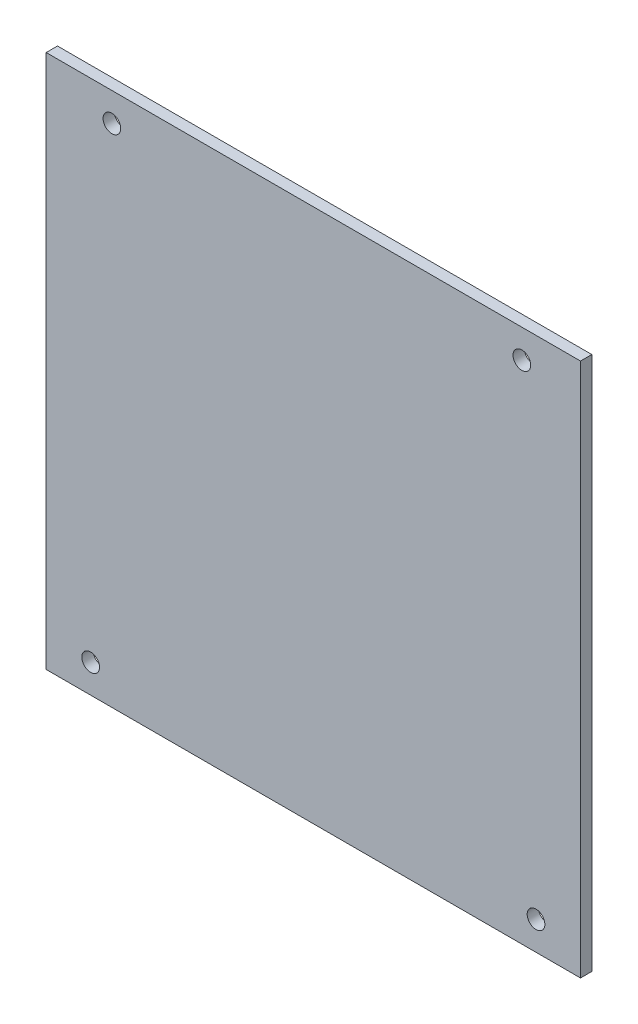
SolidWorks part; units mm, degrees
material "5052-H32"
ref_plane "Front Plane" through (0, 0, 0) normal (0, 0, 1) x (1, 0, 0)
ref_plane "Top Plane" through (0, 0, 0) normal (0, 1, 0) x (1, 0, 0)
ref_plane "Right Plane" through (0, 0, 0) normal (1, 0, 0) x (0, 0, -1)
sketch "Sketch3" plane through (0, 0, 0) normal (0, 0, 1) x (1, 0, 0)
  line L0 (-46.984, 48) -> (-46.984, -48) construction
  line L1 (-48, -48) -> (48, -48)
  line L2 (-48, -48) -> (-48, 48)
  line L3 (-48, 48) -> (48, 48)
  line L4 (48, -48) -> (48, 48)
  line L5 (-48, -48) -> (48, 48) construction
  line L6 (-48, 48) -> (48, -48) construction
  line L7 (45.968, 48) -> (45.968, -48) construction
  circle A4 centre (40.005, -42.865) radius 1.59 construction
  circle A5 centre (37.465, 42.865) radius 1.59 construction
  circle A6 centre (-36.195, 42.865) radius 1.59 construction
  circle A7 centre (-40.005, -42.865) radius 1.59 construction
  circle A8 centre (40.005, -42.865) radius 1.59
  circle A9 centre (37.465, 42.865) radius 1.59
  circle A10 centre (-36.195, 42.865) radius 1.59
  circle A11 centre (-40.005, -42.865) radius 1.59
  point P0 (0, 0)
  dimension "D1" = 96
  dimension "D2" = 2.032
  dimension "D3" = 2.032
extrude "Boss-Extrude1" add sketch "Sketch3" along normal mid plane 2.032
equation "\"side\"= 10cm"
equation "\"D1@Sketch3\"=\"side\"-2*\"t\""
equation "\"t\"= 2mm'bolt head "
equation "\"sheet_t\"= 0.08in'sheet thickness"
equation "\"D2@Sketch3\"=\"sheet_t\""
equation "\"D3@Sketch3\"=\"sheet_t\""
equation "\"bend_h\"= 10mm'bend distance to holes"
equation "\"D1@Boss-Extrude1\"=\"sheet_t\""
